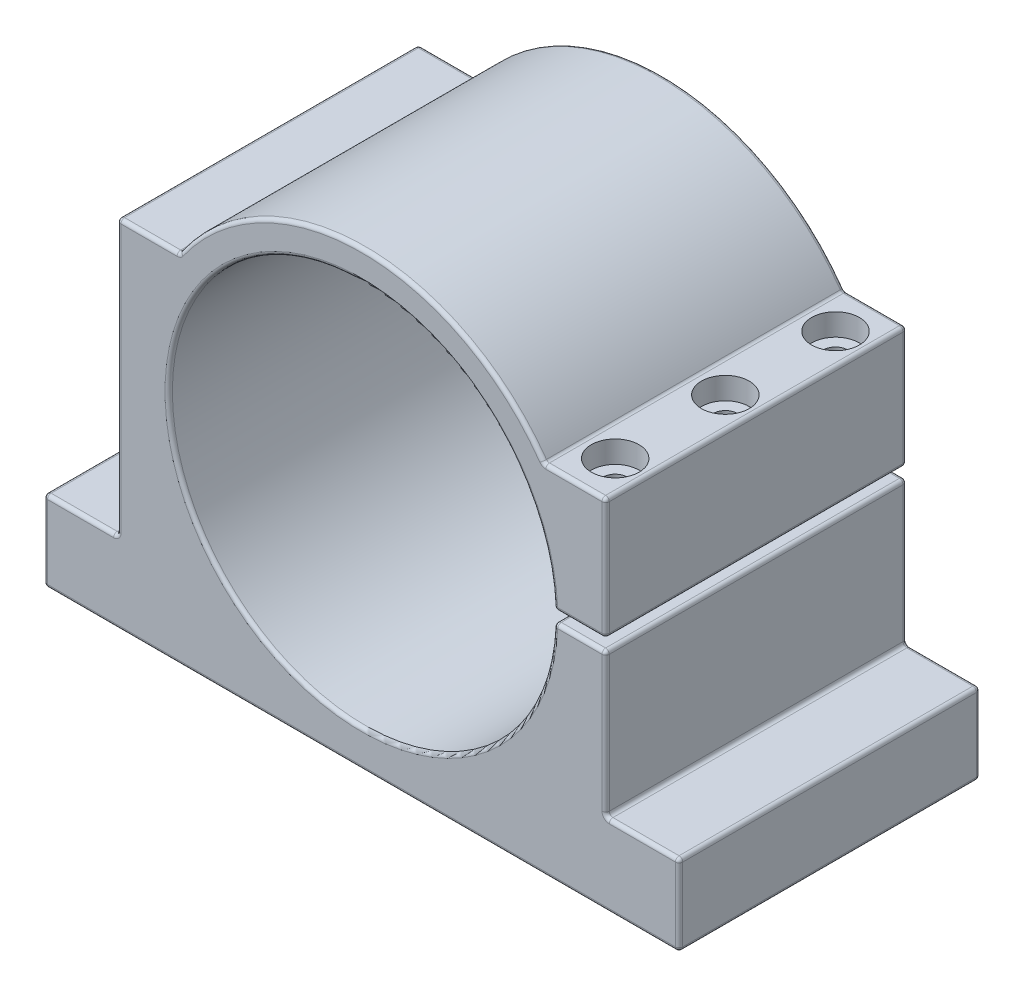
SolidWorks part; units mm, degrees
ref_plane "Спереди" through (0, 0, 0) normal (0, 0, 1) x (1, 0, 0)
ref_plane "Сверху" through (0, 0, 0) normal (0, 1, 0) x (1, 0, 0)
ref_plane "Справа" through (0, 0, 0) normal (1, 0, 0) x (0, 0, -1)
sketch "Эскиз1" plane through (0, 0, 0) normal (0, 0, 1) x (1, 0, 0)
  line L0 (0, 0) -> (0, -62.5) construction
  line L1 (86.5, -62.5) -> (-86.5, -62.5)
  line L2 (-86.5, -62.5) -> (-86.5, -40.5)
  line L3 (-86.5, -40.5) -> (-66.5, -40.5)
  line L4 (-66.5, -40.5) -> (-66.5, 34.5)
  line L5 (-66.5, 34.5) -> (-39.5727, 34.5)
  line L6 (66.5, 34.5) -> (39.5727, 34.5)
  line L7 (66.5, -40.5) -> (66.5, 34.5)
  line L8 (86.5, -40.5) -> (66.5, -40.5)
  line L9 (86.5, -62.5) -> (86.5, -40.5)
  line L10 (201.7453, 552.2596) -> (1355.0786, 552.2596) construction
  line L11 (0, 1.5) -> (95.6878, 1.5)
  line L12 (0, 1.5) -> (0, -1.5)
  line L13 (0, -1.5) -> (95.6878, -1.5)
  line L14 (95.6878, 1.5) -> (95.6878, -1.5)
  circle A0 centre (0, 0) radius 52.5
  circle A1 centre (0, 0) radius 60.5
  point P3 (0, -52.5)
  point P22 (53.0364, 34.5)
  dimension "D1" = 105
  dimension "D7" = 8
  dimension "D2" = 173
  dimension "D3" = 10
  dimension "D4" = 22
  dimension "D5" = 97
  dimension "D6" = 20
  dimension "D8" = 3
  dimension "D9" = 13.4636
extrude "Бобышка-Вытянуть1" add sketch "Эскиз1" along normal mid plane 82 contours A1 L5 L4 L3 L2 L1 L9 L8 L7 L13 | L5 A1 L13 A0 | L6 A1 L5 A0 | L11 A1 L6 A0 | A1 L11 L7 L6
sketch "Эскиз2" plane through (0, 34.5, 0) normal (0, 1, 0) x (1, 0, 0)
  line L0 (58.0995, 41) -> (58.0995, -41) construction
  line L1 (66.5, 41) -> (49.6991, 41) construction
  line L2 (66.5, -41) -> (49.6991, -41) construction
  circle A0 centre (58.0995, 30) radius 6.5
  circle A1 centre (58.0995, 0) radius 6.5
  circle A2 centre (58.0995, -30) radius 6.5
  dimension "D3" = 13
  dimension "D1" = 30
  dimension "D2" = 30
extrude "Вырез-Вытянуть1" cut sketch "Эскиз2" against normal blind 6
sketch "Эскиз3" plane through (0, 34.5, 0) normal (0, 1, 0) x (1, 0, 0)
  circle A0 centre (58.0995, 30) radius 3.25
  circle A1 centre (58.0995, 0) radius 3.25
  circle A2 centre (58.0995, -30) radius 3.25
  dimension "D1" = 6.5
extrude "Вырез-Вытянуть2" cut sketch "Эскиз3" against normal up to surface (36 mm away) up to face at (59.4893, -1.5, 0)
sketch "Эскиз4" plane through (0, -1.5, 0) normal (0, 1, 0) x (1, 0, 0)
  circle A0 centre (58.0995, 30) radius 2.35
  circle A1 centre (58.0995, 0) radius 2.35
  circle A2 centre (58.0995, -30) radius 2.35
  dimension "D1" = 4.7
extrude "Вырез-Вытянуть3" cut sketch "Эскиз4" against normal blind 30
fillet "Скругление1" radius 1 42 edges at (-86.5, -40.5, 0) (-86.5, -62.5, 0) (-66.5, -40.5, 0) (-66.5, 34.5, 0) (49.6991, 34.5, 0) (-49.6991, 34.5, 0) (66.5, 1.5, 0) (66.5, 34.5, 0) (66.5, -1.5, 0) (86.5, -62.5, 0) (86.5, -40.5, 0) (66.5, -40.5, 0) (52.4786, -1.5, 0) (52.4786, 1.5, 0) (-52.5, 0, -41) (59.4893, 1.5, -41) (66.5, 18, -41) (58.0995, 34.5, -41) (0, 60.5, -41) (-58.0995, 34.5, -41) (-66.5, -3, -41) (-76.5, -40.5, -41) (-86.5, -51.5, -41) (0, -62.5, -41) (86.5, -51.5, -41) (76.5, -40.5, -41) (66.5, -21, -41) (59.4893, -1.5, -41) (66.5, -21, 41) (76.5, -40.5, 41) (86.5, -51.5, 41) (0, -62.5, 41) (-86.5, -51.5, 41) (-76.5, -40.5, 41) (-66.5, -3, 41) (-58.0995, 34.5, 41) (0, 60.5, 41) (58.0995, 34.5, 41) (66.5, 18, 41) (59.4893, 1.5, 41) (-52.5, 0, 41) (59.4893, -1.5, 41)
